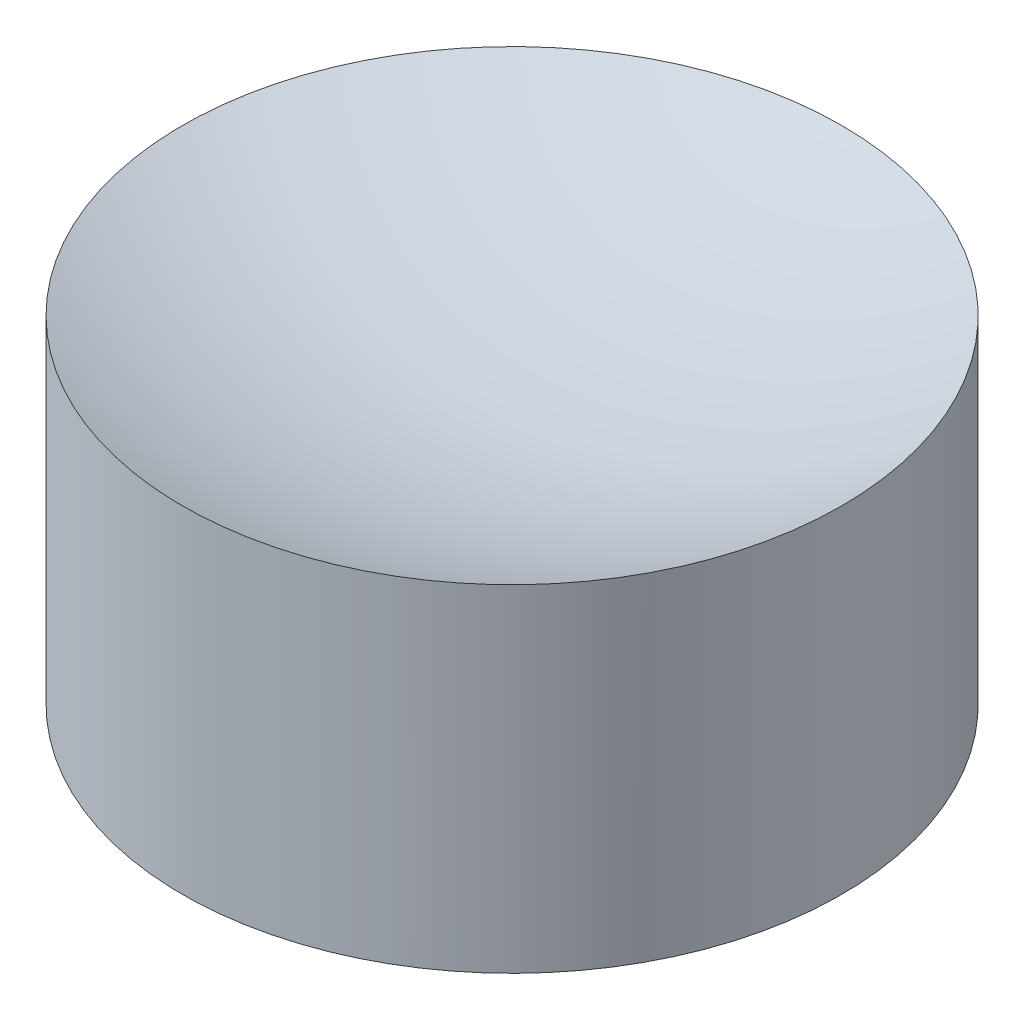
SolidWorks part; units mm, degrees
ref_plane "Front Plane" through (0, 0, 0) normal (0, 0, 1) x (1, 0, 0)
ref_plane "Top Plane" through (0, 0, 0) normal (0, 1, 0) x (1, 0, 0)
ref_plane "Right Plane" through (0, 0, 0) normal (1, 0, 0) x (0, 0, -1)
sketch "Sketch1" plane through (0, 0, 0) normal (0, 0, 1) x (1, 0, 0)
  line L0 (0, 0) -> (0, 5.7094) construction
  line L1 (2.5, 0) -> (8, 5)
  line L2 (0, 0) -> (1.5, 0)
  line L3 (0, 0) -> (0, 5)
  line L4 (0, 5) -> (1.5, 5)
  line L5 (1.5, 0) -> (1.5, 5)
  line L6 (0, 0) -> (8, 0)
  line L7 (0, 0) -> (0, 8.1697)
  line L8 (0, 8.1697) -> (8, 8.1697)
  line L9 (8, 0) -> (8, 8.1697)
  circle A0 centre (0, 26.5) radius 20
  point P13 (0, 6.5)
  point P14 (0, 0)
  dimension "D3" = 40
  dimension "D5" = 1.5
  dimension "D1" = 1.5
  dimension "D2" = 5
  dimension "D4" = 8
  dimension "D6" = 1
revolve "Revolve1" add sketch "Sketch1" angle 360 about L0
